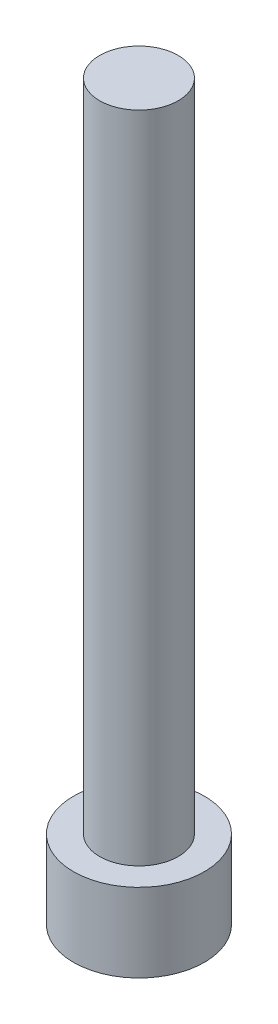
SolidWorks part; units mm, degrees
ref_plane "前视基准面" through (0, 0, 0) normal (0, 0, 1) x (1, 0, 0)
ref_plane "上视基准面" through (0, 0, 0) normal (0, 1, 0) x (1, 0, 0)
ref_plane "右视基准面" through (0, 0, 0) normal (1, 0, 0) x (0, 0, -1)
sketch "草图1" plane through (0, 0, 0) normal (0, 1, 0) x (1, 0, 0)
  circle A0 centre (0, 0) radius 2.5
  dimension "D1" = 5
extrude "凸台-拉伸1" add sketch "草图1" along normal blind 3
sketch "草图2" plane through (0, 3, 0) normal (0, 1, 0) x (1, 0, 0)
  circle A0 centre (0, 0) radius 1.5
extrude "凸台-拉伸2" add sketch "草图2" along normal blind 25
sketch "草图3" plane through (0, 0, 0) normal (0, -1, 0) x (1, 0, 0)
  line L1 (1.425, 0) -> (0.7125, 1.2341)
  line L2 (0.7125, 1.2341) -> (-0.7125, 1.2341)
  line L3 (-0.7125, 1.2341) -> (-1.425, 0)
  line L4 (-1.425, 0) -> (-0.7125, -1.2341)
  line L5 (-0.7125, -1.2341) -> (0.7125, -1.2341)
  line L6 (0.7125, -1.2341) -> (1.425, 0)
  circle A0 centre (0, 0) radius 1.2341 construction
extrude "切除-拉伸1" cut sketch "草图3" against normal blind 1.65
